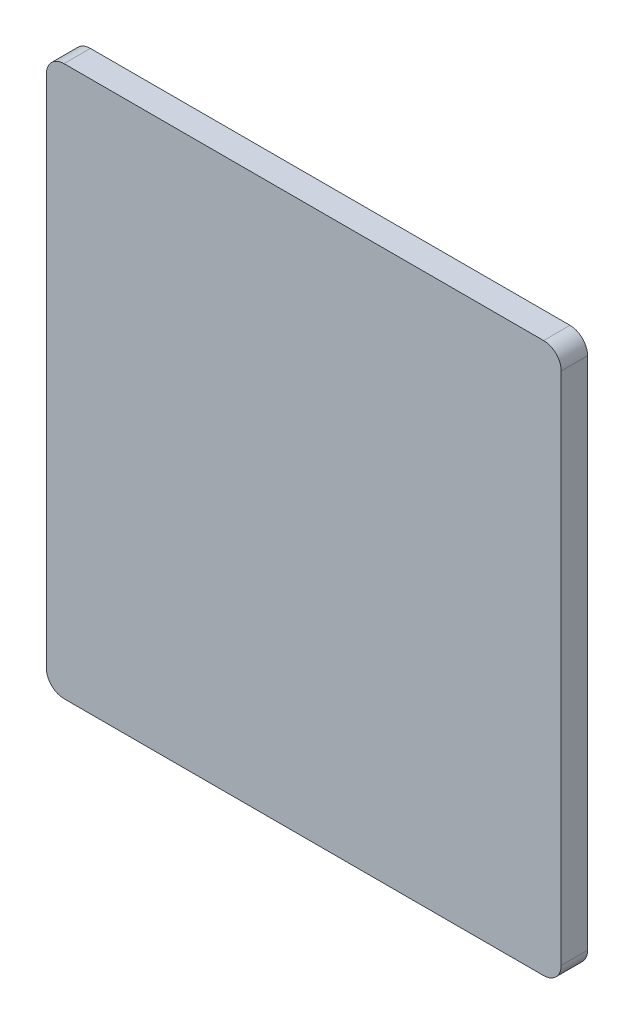
SolidWorks part; units mm, degrees
material "ABS PC"
ref_plane "Plan de face" through (0, 0, 0) normal (0, 0, 1) x (1, 0, 0)
ref_plane "Plan de dessus" through (0, 0, 0) normal (0, 1, 0) x (1, 0, 0)
ref_plane "Plan de droite" through (0, 0, 0) normal (1, 0, 0) x (0, 0, -1)
sketch "Esquisse1" plane through (0, 0, 0) normal (0, 0, 1) x (1, 0, 0)
  line L1 (2, 0) -> (56.5, 0)
  line L2 (0, 2) -> (0, 60.5)
  line L3 (2, 62.5) -> (56.5, 62.5)
  line L4 (58.5, 2) -> (58.5, 60.5)
  arc A0 (2, 0) -> (0, 2) centre (2, 2) cw
  arc A1 (56.5, 0) -> (58.5, 2) centre (56.5, 2) ccw
  arc A2 (56.5, 62.5) -> (58.5, 60.5) centre (56.5, 60.5) cw
  arc A3 (0, 60.5) -> (2, 62.5) centre (2, 60.5) cw
  point P7 (0, 0)
  point P10 (58.5, 0)
  point P13 (58.5, 62.5)
  point P16 (0, 62.5)
  dimension "D3" = 2
  dimension "D1" = 58.5
  dimension "D2" = 62.5
extrude "Boss.-Extru.1" add sketch "Esquisse1" along normal blind 3
